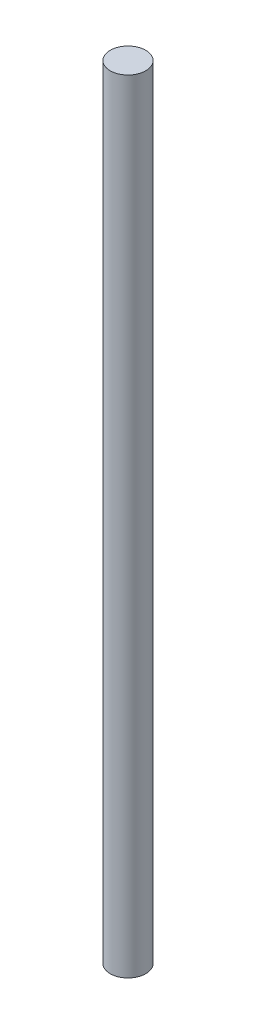
SolidWorks part; units mm, degrees
ref_plane "Plano frontal" through (0, 0, 0) normal (0, 0, 1) x (1, 0, 0)
ref_plane "Plano superior" through (0, 0, 0) normal (0, 1, 0) x (1, 0, 0)
ref_plane "Plano direito" through (0, 0, 0) normal (1, 0, 0) x (0, 0, -1)
sketch "Esboço1" plane through (0, 0, 0) normal (0, 1, 0) x (1, 0, 0)
  circle A0 centre (0, 0) radius 2.5
  dimension "D1" = 5
extrude "Ressalto-extrusão1" add sketch "Esboço1" along normal blind 110
